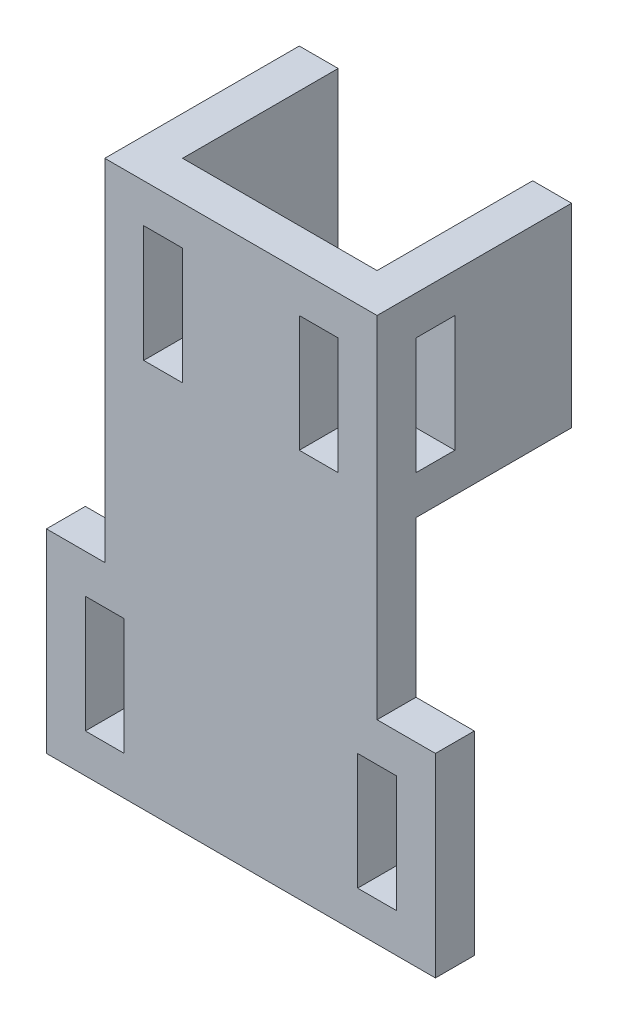
SolidWorks part; units mm, degrees
material "PLA"
ref_plane "Front Plane" through (0, 0, 0) normal (0, 0, 1) x (1, 0, 0)
ref_plane "Top Plane" through (0, 0, 0) normal (0, 1, 0) x (1, 0, 0)
ref_plane "Right Plane" through (0, 0, 0) normal (1, 0, 0) x (0, 0, -1)
sketch "Sketch1" plane through (0, 0, 0) normal (0, 0, 1) x (1, 0, 0)
  line L0 (-5, 75) -> (2.5, 25)
  line L1 (0, 0) -> (25, 0) construction
  line L2 (0, 0) -> (0, 75) construction
  line L3 (0, 75) -> (25, 75)
  line L4 (25, 0) -> (25, 75) construction
  line L5 (25, 75) -> (30, 75) construction
  line L6 (25, 75) -> (25, 100)
  line L7 (25, 100) -> (30, 100)
  line L8 (30, 75) -> (30, 100)
  line L9 (0, 75) -> (-5, 75) construction
  line L10 (0, 75) -> (0, 100)
  line L11 (0, 100) -> (-5, 100)
  line L12 (-5, 75) -> (-5, 100)
  line L13 (22.5, 0) -> (2.5, 0)
  line L14 (22.5, 0) -> (22.5, 25)
  line L15 (22.5, 25) -> (2.5, 25) construction
  line L16 (2.5, 0) -> (2.5, 25)
  line L17 (30, 75) -> (22.5, 25)
  point P15 (12.5, 25)
  point P16 (12.5, 75)
  point P17 (27.5, 75)
  dimension "D1" = 25
  dimension "D2" = 75
  dimension "D3" = 25
  dimension "D4" = 5
  dimension "D5" = 20
  dimension "D6" = 25
extrude "Boss-Extrude1" add sketch "Sketch1" along normal blind 2
sketch "Sketch2" plane through (0, 0, 0) normal (0, 0, -1) x (-1, 0, 0)
  line L0 (-30, 75) -> (-25, 75)
  line L1 (0, 75) -> (5, 75)
  line L2 (-22.5, 25) -> (-2.5, 25)
  line L12 (-25, 75) -> (-25, 100)
  line L13 (-25, 100) -> (-30, 100)
  line L14 (-30, 100) -> (-30, 75)
  line L15 (-30, 75) -> (-22.5, 25)
  line L16 (-22.5, 25) -> (-22.5, 0)
  line L17 (-22.5, 0) -> (-2.5, 0)
  line L18 (-2.5, 0) -> (-2.5, 25)
  line L19 (-2.5, 25) -> (5, 75)
  line L20 (5, 75) -> (5, 100)
  line L21 (5, 100) -> (0, 100)
  line L22 (0, 100) -> (0, 75)
  line L23 (0, 75) -> (-25, 75)
  line L24 (-25, 75) -> (-25, 100)
  line L25 (-25, 100) -> (-30, 100)
  line L26 (-30, 100) -> (-30, 75)
  line L28 (-22.5, 25) -> (-22.5, 0)
  line L29 (-22.5, 0) -> (-2.5, 0)
  line L30 (-2.5, 0) -> (-2.5, 25)
  line L32 (5, 75) -> (5, 100)
  line L33 (5, 100) -> (0, 100)
  line L34 (0, 100) -> (0, 75)
  dimension "D1" = 0
extrude "Boss-Extrude2" add sketch "Sketch2" along normal blind 20
sketch "Sketch3" plane through (0, 75, 0) normal (0, 1, 0) x (1, 0, 0)
  line L4 (25, 0) -> (0, 0)
  line L5 (0, 0) -> (0, -2)
  line L6 (0, -2) -> (25, -2)
  line L7 (25, -2) -> (25, 0)
  line L8 (25, 0) -> (0, 0)
  line L9 (0, 0) -> (0, -2)
  line L10 (0, -2) -> (25, -2)
  line L11 (25, -2) -> (25, 0)
  dimension "D1" = 0
extrude "Boss-Extrude3" add sketch "Sketch3" along normal up to surface (25 mm away) up to face at (27.5, 100, -9)
sketch "Sketch4" plane through (0, 0, 0) normal (0, 0, -1) x (-1, 0, 0)
  line L0 (-25, 75) -> (0, 75)
  line L8 (-2.5, 25) -> (5, 75)
  line L9 (5, 75) -> (0, 75)
  line L10 (0, 75) -> (0, 100)
  line L11 (0, 100) -> (-25, 100)
  line L12 (-25, 100) -> (-25, 75)
  line L13 (-25, 75) -> (-30, 75)
  line L14 (-30, 75) -> (-22.5, 25)
  line L15 (-22.5, 25) -> (-2.5, 25)
  line L18 (0, 75) -> (0, 100)
  line L19 (0, 100) -> (-25, 100)
  line L20 (-25, 100) -> (-25, 75)
  dimension "D1" = 0
extrude "Boss-Extrude4" add sketch "Sketch4" along normal blind 7
sketch "Sketch5" plane through (0, 0, 0) normal (0, 0, -1) x (-1, 0, 0)
  line L0 (5, 75) -> (5, 0)
  line L1 (5, 0) -> (-2.5, 0)
  line L2 (-22.5, 0) -> (-30, 0)
  line L3 (-30, 75) -> (-30, 0)
  line L8 (-30, 100) -> (-30, 75)
  line L9 (5, 100) -> (-30, 100)
  line L10 (5, 75) -> (5, 100)
  line L11 (-2.5, 25) -> (5, 75)
  line L12 (-2.5, 0) -> (-2.5, 25)
  line L13 (-22.5, 0) -> (-2.5, 0)
  line L14 (-22.5, 25) -> (-22.5, 0)
  line L15 (-30, 75) -> (-22.5, 25)
  line L16 (-30, 100) -> (-30, 75)
  line L17 (5, 100) -> (-30, 100)
  line L18 (5, 75) -> (5, 100)
  line L19 (-2.5, 25) -> (5, 75) construction
  line L20 (-2.5, 0) -> (-2.5, 25) construction
  line L21 (-22.5, 0) -> (-2.5, 0)
  line L22 (-22.5, 25) -> (-22.5, 0) construction
  line L23 (-30, 75) -> (-22.5, 25) construction
  point P12 (-31.1714, 0)
  dimension "D1" = 0
extrude "Boss-Extrude5" add sketch "Sketch5" against normal blind 5
sketch "Sketch6" plane through (0, 0, 5) normal (0, 0, 1) x (1, 0, 0)
  line L0 (30, 0) -> (-5, 0) construction
  line L1 (37.5, 0) -> (-12.5, 0)
  line L2 (2.5, 25) -> (22.5, 25) construction
  line L3 (-12.5, 25) -> (37.5, 25)
  line L4 (-12.5, 25) -> (-12.5, 0)
  line L5 (37.5, 25) -> (37.5, 0)
  point P4 (12.5, 25)
  point P6 (12.5, 25)
  dimension "D1" = 50
extrude "Boss-Extrude6" add sketch "Sketch6" against normal up to surface (5 mm away) up to face at (12.5, 25, 0)
sketch "Sketch8" plane through (0, 75, 0) normal (0, -1, 0) x (1, 0, 0)
  line L8 (-5, -20) -> (0, -20)
  line L9 (30, -20) -> (30, 0)
  line L10 (30, 0) -> (-5, 0)
  line L11 (-5, 0) -> (-5, -20)
  line L12 (-5, 0) -> (-5, -20)
  line L13 (-5, -20) -> (0, -20)
  line L14 (25, -20) -> (30, -20)
  line L15 (25, -7) -> (25, -20)
  line L16 (25, -20) -> (30, -20)
  line L17 (30, -20) -> (30, 0)
  line L18 (30, 0) -> (-5, 0)
  line L19 (0, -20) -> (0, -7)
  line L20 (0, -20) -> (0, -7)
  line L21 (0, -7) -> (25, -7)
  line L22 (0, -7) -> (25, -7)
  line L23 (25, -7) -> (25, -20)
  dimension "D1" = 0
extrude "Boss-Extrude7" add sketch "Sketch8" along normal blind 30
sketch "Sketch9" plane through (0, 100, 0) normal (0, 1, 0) x (1, 0, 0)
  line L8 (30, 20) -> (25, 20)
  line L9 (25, 20) -> (25, 7)
  line L10 (25, 7) -> (0, 7)
  line L11 (0, 7) -> (0, 20)
  line L12 (30, 20) -> (25, 20)
  line L13 (-5, 20) -> (-5, -5)
  line L14 (-5, -5) -> (30, -5)
  line L15 (30, -5) -> (30, 20)
  line L16 (0, 20) -> (-5, 20)
  line L17 (25, 20) -> (25, 7)
  line L18 (25, 7) -> (0, 7)
  line L19 (0, 7) -> (0, 20)
  line L20 (0, 20) -> (-5, 20)
  line L21 (-5, 20) -> (-5, -5)
  line L22 (-5, -5) -> (30, -5)
  line L23 (30, -5) -> (30, 20)
  dimension "D1" = 0
extrude "Cut-Extrude2" cut sketch "Sketch9" against normal blind 30
sketch "Sketch10" plane through (0, 0, -20) normal (0, 0, -1) x (-1, 0, 0)
  line L0 (-2.5, 25) -> (-22.5, 25) construction
  line L1 (-17.5, 25) -> (-7.5, 25) construction
  line L2 (-17.5, 25) -> (-17.5, 0)
  line L3 (-17.5, 0) -> (-7.5, 0) construction
  line L4 (-7.5, 25) -> (-7.5, 0)
  line L5 (-22.5, 0) -> (-2.5, 0) construction
  line L6 (-7.5, 0) -> (-2.5, 0)
  line L7 (-17.5, 25) -> (-22.5, 25)
  line L10 (-22.5, 25) -> (-22.5, 0)
  line L11 (-22.5, 0) -> (-2.5, 0)
  line L12 (-2.5, 0) -> (-2.5, 25)
  line L13 (-2.5, 25) -> (-22.5, 25)
  line L14 (-22.5, 25) -> (-22.5, 0)
  line L15 (-22.5, 0) -> (-17.5, 0)
  line L16 (-2.5, 0) -> (-2.5, 25)
  line L17 (-2.5, 25) -> (-7.5, 25)
  point P8 (-12.5, 25)
  point P9 (-12.5, 25)
  dimension "D1" = 10
  dimension "D2" = 0
extrude "Cut-Extrude3" cut sketch "Sketch10" against normal up to surface (20 mm away) up to face at (12.5, 20, 0)
sketch "Sketch11" plane through (0, 0, -7) normal (0, 0, -1) x (-1, 0, 0)
  line L4 (0, 45) -> (0, 70)
  line L5 (0, 70) -> (-25, 70)
  line L6 (-25, 70) -> (-25, 45)
  line L7 (-25, 45) -> (0, 45)
  line L8 (0, 45) -> (0, 70)
  line L9 (0, 70) -> (-25, 70)
  line L10 (-25, 70) -> (-25, 45)
  line L11 (-25, 45) -> (0, 45)
  dimension "D1" = 0
extrude "Cut-Extrude4" cut sketch "Sketch11" against normal up to surface (7 mm away) up to face at (12.5, 20, 0)
sketch "Sketch13" plane through (17.5, 0, 0) normal (1, 0, 0) x (0, 0, -1)
  line L0 (5, 25) -> (5, 20)
  line L1 (5, 20) -> (10, 20)
  line L2 (10, 20) -> (10, 5)
  line L3 (10, 5) -> (0, 5)
  line L4 (0, 25) -> (0, 0)
  line L5 (0, 0) -> (20, 0)
  line L6 (20, 0) -> (20, 25)
  line L7 (20, 25) -> (0, 25)
  line L8 (0, 25) -> (0, 5)
  line L9 (15, 0) -> (20, 0)
  line L10 (20, 0) -> (20, 25)
  line L11 (20, 25) -> (15, 25)
  line L12 (15, 25) -> (15, 0)
  line L13 (5, 25) -> (0, 25)
  dimension "D2" = 5
  dimension "D3" = 5
  dimension "D4" = 5
  dimension "D5" = 5
  dimension "D6" = 5
  dimension "D1" = 0
extrude "Cut-Extrude5" cut sketch "Sketch13" against normal up to surface (10 mm away) up to face at (7.5, 12.5, -10)
sketch "Sketch14" plane through (0, 0, -5) normal (0, 0, 1) x (1, 0, 0)
  line L4 (7.5, 25) -> (7.5, 20)
  line L5 (7.5, 20) -> (17.5, 20)
  line L6 (17.5, 20) -> (17.5, 25)
  line L7 (17.5, 25) -> (7.5, 25)
  line L8 (7.5, 25) -> (7.5, 20)
  line L9 (7.5, 20) -> (17.5, 20)
  line L10 (17.5, 20) -> (17.5, 25)
  line L11 (17.5, 25) -> (7.5, 25)
  dimension "D1" = 0
extrude "Boss-Extrude8" add sketch "Sketch14" along normal up to next
sketch "Sketch15" plane through (0, 0, -15) normal (0, 0, -1) x (-1, 0, 0)
  line L0 (-10, 0) -> (-10, 25)
  line L1 (-15, 25) -> (-15, 0)
  line L2 (-15, 25) -> (-17.5, 25)
  line L3 (-10, 0) -> (-7.5, 0)
  line L4 (-7.5, 0) -> (-7.5, 25)
  line L5 (-7.5, 25) -> (-17.5, 25)
  line L6 (-17.5, 25) -> (-17.5, 0)
  line L7 (-17.5, 0) -> (-7.5, 0)
  line L8 (-7.5, 0) -> (-7.5, 25)
  line L9 (-7.5, 25) -> (-10, 25)
  line L10 (-17.5, 25) -> (-17.5, 0)
  line L11 (-17.5, 0) -> (-15, 0)
  dimension "D1" = 0
  dimension "D2" = 2.5
extrude "Cut-Extrude6" cut sketch "Sketch15" against normal up to surface (15 mm away) up to face at (12.5, 26.875, 0)
sketch "Sketch16" plane through (0, 0, 5) normal (0, 0, 1) x (1, 0, 0)
  line L0 (-12.5, 25) -> (-12.5, 0) construction
  line L1 (-7.5, 20) -> (-2.5, 20)
  line L2 (-7.5, 20) -> (-7.5, 5)
  line L3 (-7.5, 5) -> (-2.5, 5)
  line L4 (-2.5, 20) -> (-2.5, 5)
  line L5 (-5, 25) -> (-12.5, 25) construction
  line L6 (37.5, 0) -> (-12.5, 0) construction
  line L7 (37.5, 0) -> (37.5, 25) construction
  line L8 (32.5, 20) -> (27.5, 20)
  line L9 (32.5, 20) -> (32.5, 5)
  line L10 (32.5, 5) -> (27.5, 5)
  line L11 (27.5, 20) -> (27.5, 5)
  point P8 (-8.75, 25)
  point P15 (-5, 5)
  dimension "D1" = 5
  dimension "D2" = 5
  dimension "D3" = 5
  dimension "D4" = 5
  dimension "D5" = 5
extrude "Cut-Extrude7" cut sketch "Sketch16" against normal through all
sketch "Sketch17" plane through (30, 0, 0) normal (1, 0, 0) x (0, 0, -1)
  line L0 (20, 45) -> (0, 45) construction
  line L1 (0, 65) -> (5, 65)
  line L2 (0, 65) -> (0, 50)
  line L3 (0, 50) -> (5, 50)
  line L4 (5, 65) -> (5, 50)
  line L5 (0, 45) -> (0, 25) construction
  line L6 (-5, 70) -> (20, 70) construction
  dimension "D1" = 5
  dimension "D2" = 5
  dimension "D3" = 5
extrude "Cut-Extrude8" cut sketch "Sketch17" against normal through all
sketch "Sketch18" plane through (0, 0, 0) normal (0, 0, -1) x (-1, 0, 0)
  line L1 (0, 65) -> (-5, 65)
  line L2 (0, 65) -> (0, 50)
  line L3 (0, 50) -> (-5, 50)
  line L4 (-5, 65) -> (-5, 50)
  line L6 (-25, 50) -> (-20, 50)
  line L7 (-25, 50) -> (-25, 65)
  line L8 (-25, 65) -> (-20, 65)
  line L9 (-20, 50) -> (-20, 65)
  dimension "D1" = 5
extrude "Cut-Extrude9" cut sketch "Sketch18" against normal through all
